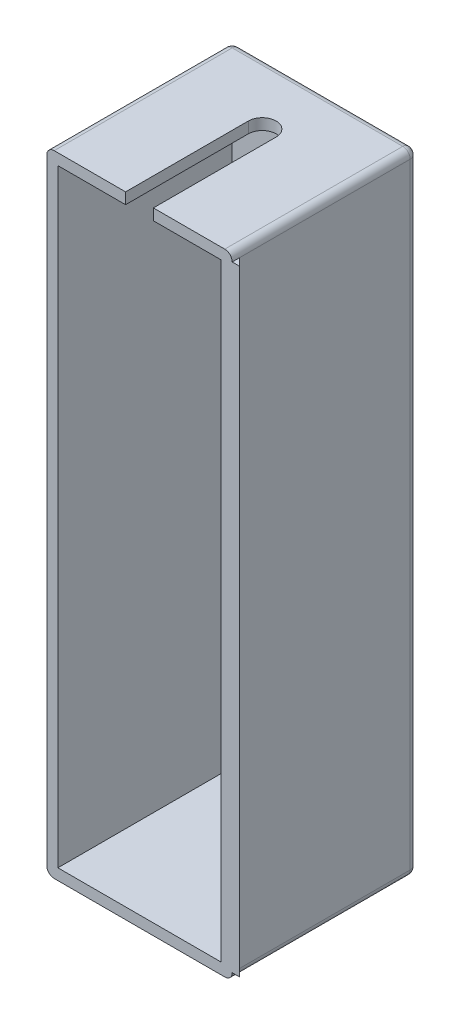
SolidWorks part; units mm, degrees
ref_plane "Front Plane" through (0, 0, 0) normal (0, 0, 1) x (1, 0, 0)
ref_plane "Top Plane" through (0, 0, 0) normal (0, 1, 0) x (1, 0, 0)
ref_plane "Right Plane" through (0, 0, 0) normal (1, 0, 0) x (0, 0, -1)
sketch "Sketch2" plane through (0, 0, 0) normal (0, 0, 1) x (1, 0, 0)
  line L1 (25, 85) -> (-25, 85)
  line L2 (25, 85) -> (25, -85)
  line L3 (25, -85) -> (-25, -85)
  line L4 (-25, 85) -> (-25, -85)
  line L5 (25, 85) -> (-25, -85) construction
  line L6 (25, -85) -> (-25, 85) construction
  point P0 (0, 0)
  dimension "D1" = 50
  dimension "D2" = 170
extrude "Boss-Extrude1" add sketch "Sketch2" along normal blind 50
sketch "Sketch3" plane through (0, 0, 50) normal (0, 0, 1) x (1, 0, 0)
  line L0 (25, 85) -> (-25, 85) construction
  line L1 (-22, 82) -> (22, 82)
  line L2 (-22, 82) -> (-22, -82)
  line L3 (-22, -82) -> (22, -82)
  line L4 (22, 82) -> (22, -82)
  line L5 (-25, -85) -> (25, -85) construction
  line L6 (25, -85) -> (25, 85) construction
  line L7 (-25, 85) -> (-25, -85) construction
  dimension "D1" = 3
  dimension "D2" = 3
  dimension "D3" = 3
  dimension "D4" = 3
extrude "Cut-Extrude1" cut sketch "Sketch3" against normal blind 47
fillet "Fillet2" radius 2 8 edges at (25, -85, 25) (25, 0, 0) (0, -85, 0) (-25, -85, 25) (-25, 0, 0) (25, 85, 25) (0, 85, 0) (-25, 85, 25)
sketch "Sketch4" plane through (25, 0, 0) normal (1, 0, 0) x (0, 0, -1)
  line L0 (-50, -83) -> (-2, -83) construction
  line L1 (-50, 83) -> (-48, 83)
  line L2 (-50, 83) -> (-50, -83)
  line L3 (-50, -83) -> (-48, -83)
  line L4 (-48, 83) -> (-48, -83)
  dimension "D1" = 2
extrude "Boss-Extrude2" add sketch "Sketch4" along normal blind 2
sketch "Sketch5" plane through (0, -83, 0) normal (0, -1, 0) x (1, 0, 0)
  line L0 (25, 48) -> (27, 50)
  line L1 (27, 50) -> (27, 48) construction
  line L2 (27, 50) -> (27, 48)
  line L3 (27, 48) -> (25, 48) construction
  line L4 (27, 48) -> (25, 48)
extrude "Cut-Extrude2" cut sketch "Sketch5" against normal blind 170
sketch "Sketch9" plane through (0, 85, 0) normal (0, 1, 0) x (1, 0, 0)
  line L0 (0, -16.8958) -> (0, -50) construction
  line L1 (23, -50) -> (-23, -50) construction
  line L2 (3.7503, -16.8958) -> (3.7503, -50)
  line L3 (-3.7503, -16.8958) -> (-3.7503, -50)
  arc A0 (3.7503, -16.8958) -> (-3.7503, -16.8958) centre (0, -16.8958) ccw
  arc A1 (-3.7503, -50) -> (3.7503, -50) centre (0, -50) ccw
  point P4 (0, -33.4479)
extrude "Cut-Extrude5" cut sketch "Sketch9" against normal blind 10
